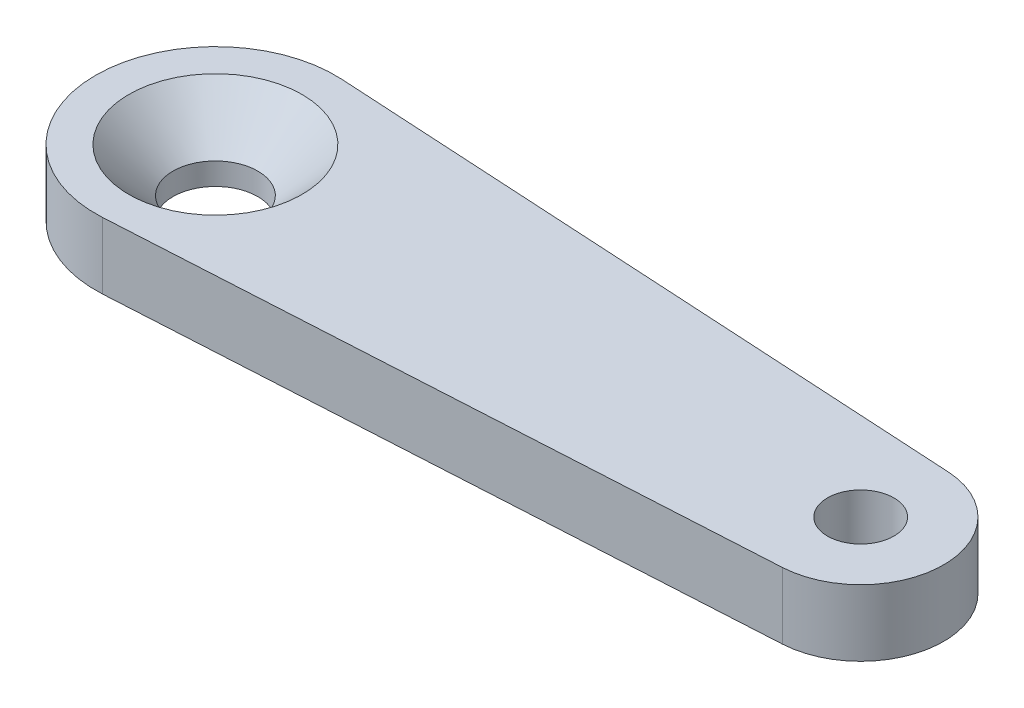
SolidWorks part; units mm, degrees
ref_plane "Спереди" through (0, 0, 0) normal (0, 0, 1) x (1, 0, 0)
ref_plane "Сверху" through (0, 0, 0) normal (0, 1, 0) x (1, 0, 0)
ref_plane "Справа" through (0, 0, 0) normal (1, 0, 0) x (0, 0, -1)
sketch "Эскиз1" plane through (0, 0, 0) normal (0, 1, 0) x (1, 0, 0)
  line L0 (0.1857, 3.2447) -> (17.6286, 2.2463)
  line L5 (17.6286, -2.2463) -> (0.1857, -3.2447)
  arc A10 (0.1857, -3.2447) -> (0.1857, 3.2447) centre (0, 0) cw
  arc A11 (17.6286, 2.2463) -> (17.6286, -2.2463) centre (17.5, 0) cw
  circle A12 centre (0, 0) radius 1.15
  circle A13 centre (17.5, 0) radius 0.9
  dimension "D2" = 2.25
  dimension "D3" = 3.25
  dimension "D4" = 2.3
  dimension "D5" = 1.8
  dimension "D1" = 17.5
extrude "Бобышка-Вытянуть1" add sketch "Эскиз1" along normal blind 1.8
chamfer "Фаска1" distance 1.2 angle 45 1 edges at (0, 1.8, 1.15)
